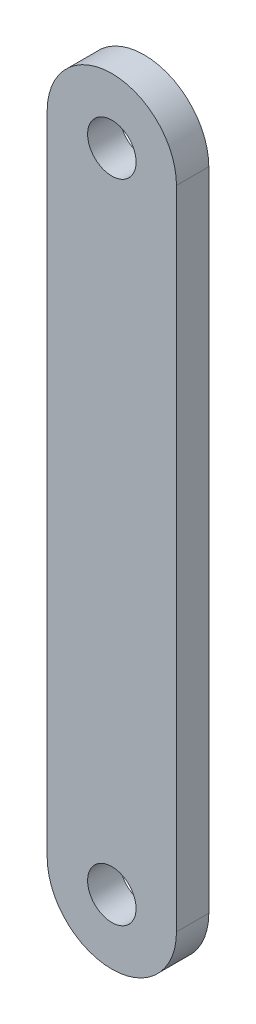
SolidWorks part; units mm, degrees
ref_plane "Front Plane" through (0, 0, 0) normal (0, 0, 1) x (1, 0, 0)
ref_plane "Top Plane" through (0, 0, 0) normal (0, 1, 0) x (1, 0, 0)
ref_plane "Right Plane" through (0, 0, 0) normal (1, 0, 0) x (0, 0, -1)
sketch "Sketch1" plane through (0, 0, 0) normal (0, 0, 1) x (1, 0, 0)
  line L0 (0, 24.5) -> (0, -30.5) construction
  line L2 (-4, 24.5) -> (-4, -15.5)
  line L4 (4, 24.5) -> (4, -15.5)
  circle A0 centre (0, 24.5) radius 1.5
  arc A1 (4, 24.5) -> (-4, 24.5) centre (0, 24.5) ccw
  circle A2 centre (0, -15.5) radius 1.5
  arc A4 (-4, -15.5) -> (4, -15.5) centre (0, -15.5) ccw
  point P0 (0, 0)
  dimension "D3" = 3
  dimension "D4" = 40
  dimension "D1" = 4
extrude "Boss-Extrude1" add sketch "Sketch1" along normal blind 2
